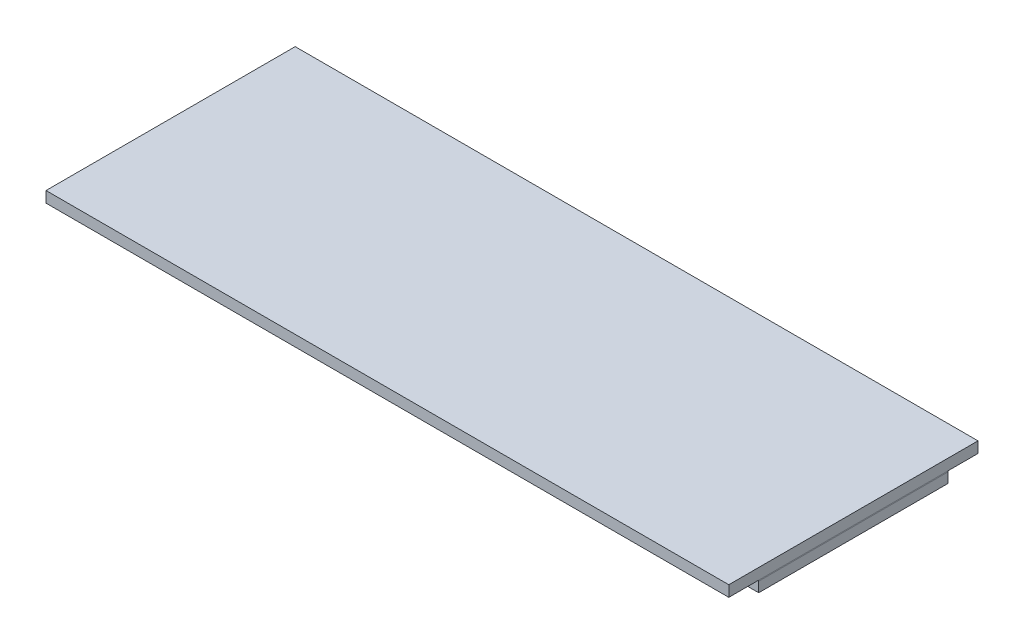
SolidWorks part; units mm, degrees
material "Glass"
ref_plane "Front Plane" through (0, 0, 0) normal (0, 0, 1) x (1, 0, 0)
ref_plane "Top Plane" through (0, 0, 0) normal (0, 1, 0) x (1, 0, 0)
ref_plane "Right Plane" through (0, 0, 0) normal (1, 0, 0) x (0, 0, -1)
sketch "Sketch1" plane through (0, 0, 0) normal (0, 1, 0) x (1, 0, 0)
  line L0 (-81.0446, 0) -> (81.0446, 0) construction
  line L1 (-34.25, 12.5) -> (34.25, 12.5)
  line L2 (-34.25, 12.5) -> (-34.25, -12.5)
  line L3 (-34.25, -12.5) -> (34.25, -12.5)
  line L4 (34.25, 12.5) -> (34.25, -12.5)
  line L5 (0, -22.2823) -> (0, 22.2823) construction
  dimension "D1" = 68.5
  dimension "D2" = 25
  dimension "D3" = 12.5
  dimension "D4" = 34.25
extrude "Boss-Extrude1" add sketch "Sketch1" along normal blind 1.1
sketch "Sketch2" plane through (0, 0, 0) normal (0, 1, 0) x (1, 0, 0)
  line L0 (-34.25, 12.5) -> (-34.25, -12.5) construction
  line L1 (-34.25, 9.5) -> (34.25, 9.5)
  line L2 (-34.25, 9.5) -> (-34.25, -9.5)
  line L3 (-34.25, -9.5) -> (34.25, -9.5)
  line L4 (34.25, 9.5) -> (34.25, -9.5)
  line L5 (34.25, -12.5) -> (34.25, 12.5) construction
  line L6 (-55, 0) -> (55, 0) construction
  dimension "D1" = 19
  dimension "D2" = 9.5
extrude "Boss-Extrude2" add sketch "Sketch2" against normal blind 0.1 separate body
sketch "Sketch3"
  dimension "D1" = 2.95
  dimension "D2" = 0.1
  dimension "D3" = 4.35
  dimension "D4" = 25.9
  dimension "D5" = 4.75
  dimension "D6" = 0.51
  dimension "D7" = 0.05
  dimension "D8" = 16
  dimension "D10" = 3.65
  dimension "D11" = 5.15
  dimension "D9" = 2
sketch "Sketch6" plane through (0, 0, 0) normal (0, 1, 0) x (1, 0, 0)
  line L1 (-27.63, -0.4) -> (-27.12, -0.4)
  line L2 (-27.63, -0.4) -> (-27.63, -0.9)
  line L3 (-27.63, -0.9) -> (-27.12, -0.9)
  line L4 (-27.12, -0.4) -> (-27.12, -0.9)
  line L5 (-27.63, -0.95) -> (-27.12, -0.95)
  line L6 (-27.63, -0.95) -> (-27.63, -1.45)
  line L7 (-27.63, -1.45) -> (-27.12, -1.45)
  line L8 (-27.12, -0.95) -> (-27.12, -1.45)
  line L9 (-27.63, -1.5) -> (-27.12, -1.5)
  line L10 (-27.63, -1.5) -> (-27.63, -2)
  line L11 (-27.63, -2) -> (-27.12, -2)
  line L12 (-27.12, -1.5) -> (-27.12, -2)
  line L13 (-27.63, -2.05) -> (-27.12, -2.05)
  line L14 (-27.63, -2.05) -> (-27.63, -2.55)
  line L15 (-27.63, -2.55) -> (-27.12, -2.55)
  line L16 (-27.12, -2.05) -> (-27.12, -2.55)
  line L17 (-27.63, -2.6) -> (-27.12, -2.6)
  line L18 (-27.63, -2.6) -> (-27.63, -3.1)
  line L19 (-27.63, -3.1) -> (-27.12, -3.1)
  line L20 (-27.12, -2.6) -> (-27.12, -3.1)
  line L21 (-27.63, -3.15) -> (-27.12, -3.15)
  line L22 (-27.63, -3.15) -> (-27.63, -3.65)
  line L23 (-27.63, -3.65) -> (-27.12, -3.65)
  line L24 (-27.12, -3.15) -> (-27.12, -3.65)
  line L25 (-27.12, -3.7) -> (-27.63, -3.7)
  line L26 (-27.12, -3.7) -> (-27.12, -4.2)
  line L27 (-27.12, -4.2) -> (-27.63, -4.2)
  line L28 (-27.63, -3.7) -> (-27.63, -4.2)
  line L29 (-28.24, -3.7) -> (-27.73, -3.7)
  line L30 (-28.24, -3.7) -> (-28.24, -4.2)
  line L31 (-28.24, -4.2) -> (-27.73, -4.2)
  line L32 (-27.73, -3.7) -> (-27.73, -4.2)
  line L33 (-27.02, -3.7) -> (-26.51, -3.7)
  line L34 (-27.02, -3.7) -> (-27.02, -4.2)
  line L35 (-27.02, -4.2) -> (-26.51, -4.2)
  line L36 (-26.51, -3.7) -> (-26.51, -4.2)
  line L37 (-28.24, -0.95) -> (-27.73, -0.95)
  line L38 (-28.24, -0.95) -> (-28.24, -1.45)
  line L39 (-28.24, -1.45) -> (-27.73, -1.45)
  line L40 (-27.73, -0.95) -> (-27.73, -1.45)
  line L41 (-22.76, -2.6) -> (-22.25, -2.6)
  line L42 (-22.76, -2.6) -> (-22.76, -3.1)
  line L43 (-22.76, -3.1) -> (-22.25, -3.1)
  line L44 (-22.25, -2.6) -> (-22.25, -3.1)
  line L45 (-22.76, -3.15) -> (-22.25, -3.15)
  line L46 (-22.76, -3.15) -> (-22.76, -3.65)
  line L47 (-22.76, -3.65) -> (-22.25, -3.65)
  line L48 (-22.25, -3.15) -> (-22.25, -3.65)
  line L49 (-23.37, -3.7) -> (-22.86, -3.7)
  line L50 (-23.37, -3.7) -> (-23.37, -4.2)
  line L51 (-23.37, -4.2) -> (-22.86, -4.2)
  line L52 (-22.86, -3.7) -> (-22.86, -4.2)
  line L53 (-23.98, -3.7) -> (-23.47, -3.7)
  line L54 (-23.98, -3.7) -> (-23.98, -4.2)
  line L55 (-23.98, -4.2) -> (-23.47, -4.2)
  line L56 (-23.47, -3.7) -> (-23.47, -4.2)
  line L57 (-24.59, -3.7) -> (-24.08, -3.7)
  line L58 (-24.59, -3.7) -> (-24.59, -4.2)
  line L59 (-24.59, -4.2) -> (-24.08, -4.2)
  line L60 (-24.08, -3.7) -> (-24.08, -4.2)
  line L61 (-25.2, -3.15) -> (-24.69, -3.15)
  line L62 (-25.2, -3.15) -> (-25.2, -3.65)
  line L63 (-25.2, -3.65) -> (-24.69, -3.65)
  line L64 (-24.69, -3.15) -> (-24.69, -3.65)
  line L65 (-25.2, -2.6) -> (-24.69, -2.6)
  line L66 (-25.2, -2.6) -> (-25.2, -3.1)
  line L67 (-25.2, -3.1) -> (-24.69, -3.1)
  line L68 (-24.69, -2.6) -> (-24.69, -3.1)
  line L69 (-25.2, -2.05) -> (-24.69, -2.05)
  line L70 (-25.2, -2.05) -> (-25.2, -2.55)
  line L71 (-25.2, -2.55) -> (-24.69, -2.55)
  line L72 (-24.69, -2.05) -> (-24.69, -2.55)
  line L73 (-23.37, -0.4) -> (-22.86, -0.4)
  line L74 (-23.37, -0.4) -> (-23.37, -0.9)
  line L75 (-23.37, -0.9) -> (-22.86, -0.9)
  line L76 (-22.86, -0.4) -> (-22.86, -0.9)
  line L77 (-23.98, -0.4) -> (-23.47, -0.4)
  line L78 (-23.98, -0.4) -> (-23.98, -0.9)
  line L79 (-23.98, -0.9) -> (-23.47, -0.9)
  line L80 (-23.47, -0.4) -> (-23.47, -0.9)
  line L81 (-24.59, -0.95) -> (-24.08, -0.95)
  line L82 (-24.59, -0.95) -> (-24.59, -1.45)
  line L83 (-24.59, -1.45) -> (-24.08, -1.45)
  line L84 (-24.08, -0.95) -> (-24.08, -1.45)
  line L85 (-25.2, -1.5) -> (-24.69, -1.5)
  line L86 (-25.2, -1.5) -> (-25.2, -2)
  line L87 (-25.2, -2) -> (-24.69, -2)
  line L88 (-24.69, -1.5) -> (-24.69, -2)
  line L89 (-24.59, -2.05) -> (-24.08, -2.05)
  line L90 (-24.59, -2.05) -> (-24.59, -2.55)
  line L91 (-24.59, -2.55) -> (-24.08, -2.55)
  line L92 (-24.08, -2.05) -> (-24.08, -2.55)
  line L93 (-23.98, -2.05) -> (-23.47, -2.05)
  line L94 (-23.98, -2.05) -> (-23.98, -2.55)
  line L95 (-23.98, -2.55) -> (-23.47, -2.55)
  line L96 (-23.47, -2.05) -> (-23.47, -2.55)
  line L97 (-23.37, -2.05) -> (-22.86, -2.05)
  line L98 (-23.37, -2.05) -> (-23.37, -2.55)
  line L99 (-23.37, -2.55) -> (-22.86, -2.55)
  line L100 (-22.86, -2.05) -> (-22.86, -2.55)
  line L101 (-21.55, -3.7) -> (-21.04, -3.7)
  line L102 (-21.55, -3.7) -> (-21.55, -4.2)
  line L103 (-21.55, -4.2) -> (-21.04, -4.2)
  line L104 (-21.04, -3.7) -> (-21.04, -4.2)
  line L105 (-20.94, -3.15) -> (-20.43, -3.15)
  line L106 (-20.94, -3.15) -> (-20.94, -3.65)
  line L107 (-20.94, -3.65) -> (-20.43, -3.65)
  line L108 (-20.43, -3.15) -> (-20.43, -3.65)
  line L109 (-20.33, -2.6) -> (-19.82, -2.6)
  line L110 (-20.33, -2.6) -> (-20.33, -3.1)
  line L111 (-20.33, -3.1) -> (-19.82, -3.1)
  line L112 (-19.82, -2.6) -> (-19.82, -3.1)
  line L113 (-19.72, -2.05) -> (-19.21, -2.05)
  line L114 (-19.72, -2.05) -> (-19.72, -2.55)
  line L115 (-19.72, -2.55) -> (-19.21, -2.55)
  line L116 (-19.21, -2.05) -> (-19.21, -2.55)
  line L117 (-19.11, -1.5) -> (-18.6, -1.5)
  line L118 (-19.11, -1.5) -> (-19.11, -2)
  line L119 (-19.11, -2) -> (-18.6, -2)
  line L120 (-18.6, -1.5) -> (-18.6, -2)
  line L121 (-20.94, -2.05) -> (-20.43, -2.05)
  line L122 (-20.94, -2.05) -> (-20.94, -2.55)
  line L123 (-20.94, -2.55) -> (-20.43, -2.55)
  line L124 (-20.43, -2.05) -> (-20.43, -2.55)
  line L125 (-21.55, -1.5) -> (-21.04, -1.5)
  line L126 (-21.55, -1.5) -> (-21.55, -2)
  line L127 (-21.55, -2) -> (-21.04, -2)
  line L128 (-21.04, -1.5) -> (-21.04, -2)
  line L129 (-19.72, -3.15) -> (-19.21, -3.15)
  line L130 (-19.72, -3.15) -> (-19.72, -3.65)
  line L131 (-19.72, -3.65) -> (-19.21, -3.65)
  line L132 (-19.21, -3.15) -> (-19.21, -3.65)
  line L133 (-19.11, -3.7) -> (-18.6, -3.7)
  line L134 (-19.11, -3.7) -> (-19.11, -4.2)
  line L135 (-19.11, -4.2) -> (-18.6, -4.2)
  line L136 (-18.6, -3.7) -> (-18.6, -4.2)
  line L137 (-17.29, -0.4) -> (-16.78, -0.4)
  line L138 (-17.29, -0.4) -> (-17.29, -0.9)
  line L139 (-17.29, -0.9) -> (-16.78, -0.9)
  line L140 (-16.78, -0.4) -> (-16.78, -0.9)
  line L141 (-16.68, -0.4) -> (-16.17, -0.4)
  line L142 (-16.68, -0.4) -> (-16.68, -0.9)
  line L143 (-16.68, -0.9) -> (-16.17, -0.9)
  line L144 (-16.17, -0.4) -> (-16.17, -0.9)
  line L145 (-16.07, -0.4) -> (-15.56, -0.4)
  line L146 (-16.07, -0.4) -> (-16.07, -0.9)
  line L147 (-16.07, -0.9) -> (-15.56, -0.9)
  line L148 (-15.56, -0.4) -> (-15.56, -0.9)
  line L149 (-15.46, -0.95) -> (-14.95, -0.95)
  line L150 (-15.46, -0.95) -> (-15.46, -1.45)
  line L151 (-15.46, -1.45) -> (-14.95, -1.45)
  line L152 (-14.95, -0.95) -> (-14.95, -1.45)
  line L153 (-15.46, -1.5) -> (-14.95, -1.5)
  line L154 (-15.46, -1.5) -> (-15.46, -2)
  line L155 (-15.46, -2) -> (-14.95, -2)
  line L156 (-14.95, -1.5) -> (-14.95, -2)
  line L157 (-16.07, -2.05) -> (-15.56, -2.05)
  line L158 (-16.07, -2.05) -> (-16.07, -2.55)
  line L159 (-16.07, -2.55) -> (-15.56, -2.55)
  line L160 (-15.56, -2.05) -> (-15.56, -2.55)
  line L161 (-16.68, -2.6) -> (-16.17, -2.6)
  line L162 (-16.68, -2.6) -> (-16.68, -3.1)
  line L163 (-16.68, -3.1) -> (-16.17, -3.1)
  line L164 (-16.17, -2.6) -> (-16.17, -3.1)
  line L165 (-17.29, -3.15) -> (-16.78, -3.15)
  line L166 (-17.29, -3.15) -> (-17.29, -3.65)
  line L167 (-17.29, -3.65) -> (-16.78, -3.65)
  line L168 (-16.78, -3.15) -> (-16.78, -3.65)
  line L169 (-17.9, -3.7) -> (-17.39, -3.7)
  line L170 (-17.9, -3.7) -> (-17.9, -4.2)
  line L171 (-17.9, -4.2) -> (-17.39, -4.2)
  line L172 (-17.39, -3.7) -> (-17.39, -4.2)
  line L173 (-17.29, -3.7) -> (-16.78, -3.7)
  line L174 (-17.29, -3.7) -> (-17.29, -4.2)
  line L175 (-17.29, -4.2) -> (-16.78, -4.2)
  line L176 (-16.78, -3.7) -> (-16.78, -4.2)
  line L177 (-16.68, -3.7) -> (-16.17, -3.7)
  line L178 (-16.68, -3.7) -> (-16.68, -4.2)
  line L179 (-16.68, -4.2) -> (-16.17, -4.2)
  line L180 (-16.17, -3.7) -> (-16.17, -4.2)
  line L181 (-16.07, -4.2) -> (-15.56, -4.2)
  line L182 (-16.07, -4.2) -> (-16.07, -3.7)
  line L183 (-16.07, -3.7) -> (-15.56, -3.7)
  line L184 (-15.56, -4.2) -> (-15.56, -3.7)
  line L185 (-15.46, -4.2) -> (-14.95, -4.2)
  line L186 (-15.46, -4.2) -> (-15.46, -3.7)
  line L187 (-15.46, -3.7) -> (-14.95, -3.7)
  line L188 (-14.95, -4.2) -> (-14.95, -3.7)
  line L189 (-17.9, -0.95) -> (-17.39, -0.95)
  line L190 (-17.9, -0.95) -> (-17.9, -1.45)
  line L191 (-17.9, -1.45) -> (-17.39, -1.45)
  line L192 (-17.39, -0.95) -> (-17.39, -1.45)
  line L193 (-10.6, -0.4) -> (-10.09, -0.4)
  line L194 (-10.6, -0.4) -> (-10.6, -0.9)
  line L195 (-10.6, -0.9) -> (-10.09, -0.9)
  line L196 (-10.09, -0.4) -> (-10.09, -0.9)
  line L197 (-10.6, -0.95) -> (-10.09, -0.95)
  line L198 (-10.6, -0.95) -> (-10.6, -1.45)
  line L199 (-10.6, -1.45) -> (-10.09, -1.45)
  line L200 (-10.09, -0.95) -> (-10.09, -1.45)
  line L201 (-10.6, -1.5) -> (-10.09, -1.5)
  line L202 (-10.6, -1.5) -> (-10.6, -2)
  line L203 (-10.6, -2) -> (-10.09, -2)
  line L204 (-10.09, -1.5) -> (-10.09, -2)
  line L205 (-10.6, -2.05) -> (-10.09, -2.05)
  line L206 (-10.6, -2.05) -> (-10.6, -2.55)
  line L207 (-10.6, -2.55) -> (-10.09, -2.55)
  line L208 (-10.09, -2.05) -> (-10.09, -2.55)
  line L209 (-10.6, -2.6) -> (-10.09, -2.6)
  line L210 (-10.6, -2.6) -> (-10.6, -3.1)
  line L211 (-10.6, -3.1) -> (-10.09, -3.1)
  line L212 (-10.09, -2.6) -> (-10.09, -3.1)
  line L213 (-10.6, -3.15) -> (-10.09, -3.15)
  line L214 (-10.6, -3.15) -> (-10.6, -3.65)
  line L215 (-10.6, -3.65) -> (-10.09, -3.65)
  line L216 (-10.09, -3.15) -> (-10.09, -3.65)
  line L217 (-10.6, -3.7) -> (-10.09, -3.7)
  line L218 (-10.6, -3.7) -> (-10.6, -4.2)
  line L219 (-10.6, -4.2) -> (-10.09, -4.2)
  line L220 (-10.09, -3.7) -> (-10.09, -4.2)
  line L221 (-9.99, -3.7) -> (-9.48, -3.7)
  line L222 (-9.99, -3.7) -> (-9.99, -4.2)
  line L223 (-9.99, -4.2) -> (-9.48, -4.2)
  line L224 (-9.48, -3.7) -> (-9.48, -4.2)
  line L225 (-9.38, -3.7) -> (-8.87, -3.7)
  line L226 (-9.38, -3.7) -> (-9.38, -4.2)
  line L227 (-9.38, -4.2) -> (-8.87, -4.2)
  line L228 (-8.87, -3.7) -> (-8.87, -4.2)
  line L229 (-8.77, -3.7) -> (-8.26, -3.7)
  line L230 (-8.77, -3.7) -> (-8.77, -4.2)
  line L231 (-8.77, -4.2) -> (-8.26, -4.2)
  line L232 (-8.26, -3.7) -> (-8.26, -4.2)
  line L233 (-8.16, -3.7) -> (-7.65, -3.7)
  line L234 (-8.16, -3.7) -> (-8.16, -4.2)
  line L235 (-8.16, -4.2) -> (-7.65, -4.2)
  line L236 (-7.65, -3.7) -> (-7.65, -4.2)
  line L237 (-6.34, -0.4) -> (-5.83, -0.4)
  line L238 (-6.34, -0.4) -> (-6.34, -0.9)
  line L239 (-6.34, -0.9) -> (-5.83, -0.9)
  line L240 (-5.83, -0.4) -> (-5.83, -0.9)
  line L241 (-5.73, -0.4) -> (-5.22, -0.4)
  line L242 (-5.73, -0.4) -> (-5.73, -0.9)
  line L243 (-5.73, -0.9) -> (-5.22, -0.9)
  line L244 (-5.22, -0.4) -> (-5.22, -0.9)
  line L245 (-5.12, -0.4) -> (-4.61, -0.4)
  line L246 (-5.12, -0.4) -> (-5.12, -0.9)
  line L247 (-5.12, -0.9) -> (-4.61, -0.9)
  line L248 (-4.61, -0.4) -> (-4.61, -0.9)
  line L249 (-4.51, -0.95) -> (-4, -0.95)
  line L250 (-4.51, -0.95) -> (-4.51, -1.45)
  line L251 (-4.51, -1.45) -> (-4, -1.45)
  line L252 (-4, -0.95) -> (-4, -1.45)
  line L253 (-6.95, -0.95) -> (-6.44, -0.95)
  line L254 (-6.95, -0.95) -> (-6.95, -1.45)
  line L255 (-6.95, -1.45) -> (-6.44, -1.45)
  line L256 (-6.44, -0.95) -> (-6.44, -1.45)
  line L257 (-6.95, -1.5) -> (-6.44, -1.5)
  line L258 (-6.95, -1.5) -> (-6.95, -2)
  line L259 (-6.95, -2) -> (-6.44, -2)
  line L260 (-6.44, -1.5) -> (-6.44, -2)
  line L261 (-6.95, -2.05) -> (-6.44, -2.05)
  line L262 (-6.95, -2.05) -> (-6.95, -2.55)
  line L263 (-6.95, -2.55) -> (-6.44, -2.55)
  line L264 (-6.44, -2.05) -> (-6.44, -2.55)
  line L265 (-6.95, -2.6) -> (-6.44, -2.6)
  line L266 (-6.95, -2.6) -> (-6.95, -3.1)
  line L267 (-6.95, -3.1) -> (-6.44, -3.1)
  line L268 (-6.44, -2.6) -> (-6.44, -3.1)
  line L269 (-6.95, -3.15) -> (-6.44, -3.15)
  line L270 (-6.95, -3.15) -> (-6.95, -3.65)
  line L271 (-6.95, -3.65) -> (-6.44, -3.65)
  line L272 (-6.44, -3.15) -> (-6.44, -3.65)
  line L273 (-6.34, -3.7) -> (-5.83, -3.7)
  line L274 (-6.34, -3.7) -> (-6.34, -4.2)
  line L275 (-6.34, -4.2) -> (-5.83, -4.2)
  line L276 (-5.83, -3.7) -> (-5.83, -4.2)
  line L277 (-5.73, -4.2) -> (-5.22, -4.2)
  line L278 (-5.73, -4.2) -> (-5.73, -3.7)
  line L279 (-5.73, -3.7) -> (-5.22, -3.7)
  line L280 (-5.22, -4.2) -> (-5.22, -3.7)
  line L281 (-5.12, -3.7) -> (-4.61, -3.7)
  line L282 (-5.12, -3.7) -> (-5.12, -4.2)
  line L283 (-5.12, -4.2) -> (-4.61, -4.2)
  line L284 (-4.61, -3.7) -> (-4.61, -4.2)
  line L285 (-4.51, -3.15) -> (-4, -3.15)
  line L286 (-4.51, -3.15) -> (-4.51, -3.65)
  line L287 (-4.51, -3.65) -> (-4, -3.65)
  line L288 (-4, -3.15) -> (-4, -3.65)
  line L289 (-3.3, -0.4) -> (-2.79, -0.4)
  line L290 (-3.3, -0.4) -> (-3.3, -0.9)
  line L291 (-3.3, -0.9) -> (-2.79, -0.9)
  line L292 (-2.79, -0.4) -> (-2.79, -0.9)
  line L293 (-2.69, -0.4) -> (-2.18, -0.4)
  line L294 (-2.69, -0.4) -> (-2.69, -0.9)
  line L295 (-2.69, -0.9) -> (-2.18, -0.9)
  line L296 (-2.18, -0.4) -> (-2.18, -0.9)
  line L297 (-2.08, -0.4) -> (-1.57, -0.4)
  line L298 (-2.08, -0.4) -> (-2.08, -0.9)
  line L299 (-2.08, -0.9) -> (-1.57, -0.9)
  line L300 (-1.57, -0.4) -> (-1.57, -0.9)
  line L301 (-1.47, -0.95) -> (-0.96, -0.95)
  line L302 (-1.47, -0.95) -> (-1.47, -1.45)
  line L303 (-1.47, -1.45) -> (-0.96, -1.45)
  line L304 (-0.96, -0.95) -> (-0.96, -1.45)
  line L305 (-0.86, -1.5) -> (-0.35, -1.5)
  line L306 (-0.86, -1.5) -> (-0.86, -2)
  line L307 (-0.86, -2) -> (-0.35, -2)
  line L308 (-0.35, -1.5) -> (-0.35, -2)
  line L309 (-3.3, -0.95) -> (-2.79, -0.95)
  line L310 (-3.3, -0.95) -> (-3.3, -1.45)
  line L311 (-3.3, -1.45) -> (-2.79, -1.45)
  line L312 (-2.79, -0.95) -> (-2.79, -1.45)
  line L313 (-3.3, -1.5) -> (-2.79, -1.5)
  line L314 (-3.3, -1.5) -> (-3.3, -2)
  line L315 (-3.3, -2) -> (-2.79, -2)
  line L316 (-2.79, -1.5) -> (-2.79, -2)
  line L317 (-3.3, -2.05) -> (-2.79, -2.05)
  line L318 (-3.3, -2.05) -> (-3.3, -2.55)
  line L319 (-3.3, -2.55) -> (-2.79, -2.55)
  line L320 (-2.79, -2.05) -> (-2.79, -2.55)
  line L321 (-3.3, -2.6) -> (-2.79, -2.6)
  line L322 (-3.3, -2.6) -> (-3.3, -3.1)
  line L323 (-3.3, -3.1) -> (-2.79, -3.1)
  line L324 (-2.79, -2.6) -> (-2.79, -3.1)
  line L325 (-3.3, -3.15) -> (-2.79, -3.15)
  line L326 (-3.3, -3.15) -> (-3.3, -3.65)
  line L327 (-3.3, -3.65) -> (-2.79, -3.65)
  line L328 (-2.79, -3.15) -> (-2.79, -3.65)
  line L329 (-3.3, -3.7) -> (-2.79, -3.7)
  line L330 (-3.3, -3.7) -> (-3.3, -4.2)
  line L331 (-3.3, -4.2) -> (-2.79, -4.2)
  line L332 (-2.79, -3.7) -> (-2.79, -4.2)
  line L333 (-2.69, -4.2) -> (-2.18, -4.2)
  line L334 (-2.69, -4.2) -> (-2.69, -3.7)
  line L335 (-2.69, -3.7) -> (-2.18, -3.7)
  line L336 (-2.18, -4.2) -> (-2.18, -3.7)
  line L337 (-2.08, -4.2) -> (-1.57, -4.2)
  line L338 (-2.08, -4.2) -> (-2.08, -3.7)
  line L339 (-2.08, -3.7) -> (-1.57, -3.7)
  line L340 (-1.57, -4.2) -> (-1.57, -3.7)
  line L349 (-1.47, -3.15) -> (-0.96, -3.15)
  line L350 (-1.47, -3.15) -> (-1.47, -3.65)
  line L351 (-1.47, -3.65) -> (-0.96, -3.65)
  line L352 (-0.96, -3.15) -> (-0.96, -3.65)
  line L353 (-0.86, -2.6) -> (-0.35, -2.6)
  line L354 (-0.86, -2.6) -> (-0.86, -3.1)
  line L355 (-0.86, -3.1) -> (-0.35, -3.1)
  line L356 (-0.35, -2.6) -> (-0.35, -3.1)
  line L357 (-0.86, -2.05) -> (-0.35, -2.05)
  line L358 (-0.86, -2.05) -> (-0.86, -2.55)
  line L359 (-0.86, -2.55) -> (-0.35, -2.55)
  line L360 (-0.35, -2.05) -> (-0.35, -2.55)
  point P458 (0, 0)
  point P459 (0, 0)
extrude "16x2 LCD" cut sketch "Sketch6" against normal blind 1
sketch "Sketch7" plane through (0, 0, 0) normal (0, 1, 0) x (1, 0, 0)
  line L0 (12.52, -2) -> (13.03, -2) construction
  line L1 (4, -0.4) -> (4.51, -0.4)
  line L2 (4, -0.4) -> (4, -0.9)
  line L3 (4, -0.9) -> (4.51, -0.9)
  line L4 (4.51, -0.4) -> (4.51, -0.9)
  line L5 (4.61, -0.4) -> (5.12, -0.4)
  line L6 (4.61, -0.4) -> (4.61, -0.9)
  line L7 (4.61, -0.9) -> (5.12, -0.9)
  line L8 (5.12, -0.4) -> (5.12, -0.9)
  line L9 (5.22, -0.4) -> (5.73, -0.4)
  line L10 (5.22, -0.4) -> (5.22, -0.9)
  line L11 (5.22, -0.9) -> (5.73, -0.9)
  line L12 (5.73, -0.4) -> (5.73, -0.9)
  line L13 (5.83, -0.95) -> (6.34, -0.95)
  line L14 (5.83, -0.95) -> (5.83, -1.45)
  line L15 (5.83, -1.45) -> (6.34, -1.45)
  line L16 (6.34, -0.95) -> (6.34, -1.45)
  line L17 (6.44, -1.5) -> (6.95, -1.5)
  line L18 (6.44, -1.5) -> (6.44, -2)
  line L19 (6.44, -2) -> (6.95, -2)
  line L20 (6.95, -1.5) -> (6.95, -2)
  line L21 (6.44, -2.05) -> (6.95, -2.05)
  line L22 (6.44, -2.05) -> (6.44, -2.55)
  line L23 (6.44, -2.55) -> (6.95, -2.55)
  line L24 (6.95, -2.05) -> (6.95, -2.55)
  line L25 (6.44, -2.6) -> (6.95, -2.6)
  line L26 (6.44, -2.6) -> (6.44, -3.1)
  line L27 (6.44, -3.1) -> (6.95, -3.1)
  line L28 (6.95, -2.6) -> (6.95, -3.1)
  line L29 (5.83, -3.15) -> (6.34, -3.15)
  line L30 (5.83, -3.15) -> (5.83, -3.65)
  line L31 (5.83, -3.65) -> (6.34, -3.65)
  line L32 (6.34, -3.15) -> (6.34, -3.65)
  line L33 (5.22, -3.7) -> (5.73, -3.7)
  line L34 (5.22, -3.7) -> (5.22, -4.2)
  line L35 (5.22, -4.2) -> (5.73, -4.2)
  line L36 (5.73, -3.7) -> (5.73, -4.2)
  line L37 (4.61, -3.7) -> (5.12, -3.7)
  line L38 (4.61, -3.7) -> (4.61, -4.2)
  line L39 (4.61, -4.2) -> (5.12, -4.2)
  line L40 (5.12, -3.7) -> (5.12, -4.2)
  line L41 (4, -3.7) -> (4.51, -3.7)
  line L42 (4, -3.7) -> (4, -4.2)
  line L43 (4, -4.2) -> (4.51, -4.2)
  line L44 (4.51, -3.7) -> (4.51, -4.2)
  line L45 (4, -3.15) -> (4.51, -3.15)
  line L46 (4, -3.15) -> (4, -3.65)
  line L47 (4, -3.65) -> (4.51, -3.65)
  line L48 (4.51, -3.15) -> (4.51, -3.65)
  line L49 (4, -2.6) -> (4.51, -2.6)
  line L50 (4, -2.6) -> (4, -3.1)
  line L51 (4, -3.1) -> (4.51, -3.1)
  line L52 (4.51, -2.6) -> (4.51, -3.1)
  line L53 (4, -2.05) -> (4.51, -2.05)
  line L54 (4, -2.05) -> (4, -2.55)
  line L55 (4, -2.55) -> (4.51, -2.55)
  line L56 (4.51, -2.05) -> (4.51, -2.55)
  line L57 (4, -1.5) -> (4.51, -1.5)
  line L58 (4, -1.5) -> (4, -2)
  line L59 (4, -2) -> (4.51, -2)
  line L60 (4.51, -1.5) -> (4.51, -2)
  line L61 (4, -0.95) -> (4.51, -0.95)
  line L62 (4, -0.95) -> (4, -1.45)
  line L63 (4, -1.45) -> (4.51, -1.45)
  line L64 (4.51, -0.95) -> (4.51, -1.45)
  line L65 (8.87, -0.4) -> (9.38, -0.4)
  line L66 (8.87, -0.4) -> (8.87, -0.9)
  line L67 (8.87, -0.9) -> (9.38, -0.9)
  line L68 (9.38, -0.4) -> (9.38, -0.9)
  line L69 (8.87, -1.5) -> (9.38, -1.5)
  line L70 (8.87, -1.5) -> (8.87, -2)
  line L71 (8.87, -2) -> (9.38, -2)
  line L72 (9.38, -1.5) -> (9.38, -2)
  line L73 (8.26, -1.5) -> (8.77, -1.5)
  line L74 (8.26, -1.5) -> (8.26, -2)
  line L75 (8.26, -2) -> (8.77, -2)
  line L76 (8.77, -1.5) -> (8.77, -2)
  line L77 (8.87, -2.05) -> (9.38, -2.05)
  line L78 (8.87, -2.05) -> (8.87, -2.55)
  line L79 (8.87, -2.55) -> (9.38, -2.55)
  line L80 (9.38, -2.05) -> (9.38, -2.55)
  line L81 (8.87, -2.6) -> (9.38, -2.6)
  line L82 (8.87, -2.6) -> (8.87, -3.1)
  line L83 (8.87, -3.1) -> (9.38, -3.1)
  line L84 (9.38, -2.6) -> (9.38, -3.1)
  line L85 (8.87, -3.15) -> (9.38, -3.15)
  line L86 (8.87, -3.15) -> (8.87, -3.65)
  line L87 (8.87, -3.65) -> (9.38, -3.65)
  line L88 (9.38, -3.15) -> (9.38, -3.65)
  line L89 (8.26, -3.7) -> (8.77, -3.7)
  line L90 (8.26, -3.7) -> (8.26, -4.2)
  line L91 (8.26, -4.2) -> (8.77, -4.2)
  line L92 (8.77, -3.7) -> (8.77, -4.2)
  line L93 (8.87, -3.7) -> (9.38, -3.7)
  line L94 (8.87, -3.7) -> (8.87, -4.2)
  line L95 (8.87, -4.2) -> (9.38, -4.2)
  line L96 (9.38, -3.7) -> (9.38, -4.2)
  line L97 (9.48, -3.7) -> (9.99, -3.7)
  line L98 (9.48, -3.7) -> (9.48, -4.2)
  line L99 (9.48, -4.2) -> (9.99, -4.2)
  line L100 (9.99, -3.7) -> (9.99, -4.2)
  line L101 (11.91, -1.5) -> (12.42, -1.5)
  line L102 (11.91, -1.5) -> (11.91, -2)
  line L103 (11.91, -2) -> (12.42, -2)
  line L104 (12.42, -1.5) -> (12.42, -2)
  line L105 (12.52, -1.5) -> (13.03, -1.5)
  line L106 (12.52, -1.5) -> (12.52, -2)
  line L107 (12.52, -2) -> (13.03, -2)
  line L108 (13.03, -1.5) -> (13.03, -2)
  line L110 (13.13, -1.5) -> (13.64, -1.5)
  line L111 (13.13, -1.5) -> (13.13, -2)
  line L112 (13.13, -2) -> (13.64, -2)
  line L113 (13.64, -1.5) -> (13.64, -2)
  line L114 (11.91, -2.6) -> (12.42, -2.6)
  line L115 (11.91, -2.6) -> (11.91, -3.1)
  line L116 (11.91, -3.1) -> (12.42, -3.1)
  line L117 (12.42, -2.6) -> (12.42, -3.1)
  line L118 (12.52, -2.6) -> (13.03, -2.6)
  line L119 (12.52, -2.6) -> (12.52, -3.1)
  line L120 (12.52, -3.1) -> (13.03, -3.1)
  line L121 (13.03, -2.6) -> (13.03, -3.1)
  line L122 (13.13, -2.6) -> (13.64, -2.6)
  line L123 (13.13, -2.6) -> (13.13, -3.1)
  line L124 (13.13, -3.1) -> (13.64, -3.1)
  line L125 (13.64, -2.6) -> (13.64, -3.1)
  line L126 (13.64, -3.7) -> (13.13, -3.7)
  line L127 (13.64, -3.7) -> (13.64, -4.2)
  line L128 (13.64, -4.2) -> (13.13, -4.2)
  line L129 (13.13, -3.7) -> (13.13, -4.2)
  line L130 (13.03, -3.7) -> (12.52, -3.7)
  line L131 (13.03, -3.7) -> (13.03, -4.2)
  line L132 (13.03, -4.2) -> (12.52, -4.2)
  line L133 (12.52, -3.7) -> (12.52, -4.2)
  line L134 (11.91, -3.7) -> (12.42, -3.7)
  line L135 (11.91, -3.7) -> (11.91, -4.2)
  line L136 (11.91, -4.2) -> (12.42, -4.2)
  line L137 (12.42, -3.7) -> (12.42, -4.2)
  line L138 (11.3, -2.05) -> (11.81, -2.05)
  line L139 (11.3, -2.05) -> (11.3, -2.55)
  line L140 (11.3, -2.55) -> (11.81, -2.55)
  line L141 (11.81, -2.05) -> (11.81, -2.55)
  line L142 (13.74, -3.15) -> (14.25, -3.15)
  line L143 (13.74, -3.15) -> (13.74, -3.65)
  line L144 (13.74, -3.65) -> (14.25, -3.65)
  line L145 (14.25, -3.15) -> (14.25, -3.65)
  line L146 (11.3, -3.7) -> (11.81, -3.7)
  line L147 (11.3, -3.7) -> (11.3, -4.2)
  line L148 (11.3, -4.2) -> (11.81, -4.2)
  line L149 (11.81, -3.7) -> (11.81, -4.2)
  line L150 (14.95, -4.25) -> (15.46, -4.25)
  line L151 (14.95, -4.25) -> (14.95, -4.75)
  line L152 (14.95, -4.75) -> (15.46, -4.75)
  line L153 (15.46, -4.25) -> (15.46, -4.75)
  line L154 (14.95, -3.7) -> (15.46, -3.7)
  line L155 (14.95, -3.7) -> (14.95, -4.2)
  line L156 (14.95, -4.2) -> (15.46, -4.2)
  line L157 (15.46, -3.7) -> (15.46, -4.2)
  line L158 (14.95, -3.15) -> (15.46, -3.15)
  line L159 (14.95, -3.15) -> (14.95, -3.65)
  line L160 (14.95, -3.65) -> (15.46, -3.65)
  line L161 (15.46, -3.15) -> (15.46, -3.65)
  line L162 (14.95, -2.6) -> (15.46, -2.6)
  line L163 (14.95, -2.6) -> (14.95, -3.1)
  line L164 (14.95, -3.1) -> (15.46, -3.1)
  line L165 (15.46, -2.6) -> (15.46, -3.1)
  line L166 (14.95, -2.05) -> (15.46, -2.05)
  line L167 (14.95, -2.05) -> (14.95, -2.55)
  line L168 (14.95, -2.55) -> (15.46, -2.55)
  line L169 (15.46, -2.05) -> (15.46, -2.55)
  line L170 (14.95, -1.5) -> (15.46, -1.5)
  line L171 (14.95, -1.5) -> (14.95, -2)
  line L172 (14.95, -2) -> (15.46, -2)
  line L173 (15.46, -1.5) -> (15.46, -2)
  line L174 (15.56, -2.05) -> (16.07, -2.05)
  line L175 (15.56, -2.05) -> (15.56, -2.55)
  line L176 (15.56, -2.55) -> (16.07, -2.55)
  line L177 (16.07, -2.05) -> (16.07, -2.55)
  line L178 (16.17, -1.5) -> (16.68, -1.5)
  line L179 (16.17, -1.5) -> (16.17, -2)
  line L180 (16.17, -2) -> (16.68, -2)
  line L181 (16.68, -1.5) -> (16.68, -2)
  line L182 (16.78, -1.5) -> (17.29, -1.5)
  line L183 (16.78, -1.5) -> (16.78, -2)
  line L184 (16.78, -2) -> (17.29, -2)
  line L185 (17.29, -1.5) -> (17.29, -2)
  line L186 (17.39, -2.05) -> (17.9, -2.05)
  line L187 (17.39, -2.05) -> (17.39, -2.55)
  line L188 (17.39, -2.55) -> (17.9, -2.55)
  line L189 (17.9, -2.05) -> (17.9, -2.55)
  line L190 (17.39, -2.6) -> (17.9, -2.6)
  line L191 (17.39, -2.6) -> (17.39, -3.1)
  line L192 (17.39, -3.1) -> (17.9, -3.1)
  line L193 (17.9, -2.6) -> (17.9, -3.1)
  line L194 (15.56, -3.15) -> (16.07, -3.15)
  line L195 (15.56, -3.15) -> (15.56, -3.65)
  line L196 (15.56, -3.65) -> (16.07, -3.65)
  line L197 (16.07, -3.15) -> (16.07, -3.65)
  line L198 (16.17, -3.15) -> (16.68, -3.15)
  line L199 (16.17, -3.15) -> (16.17, -3.65)
  line L200 (16.17, -3.65) -> (16.68, -3.65)
  line L201 (16.68, -3.15) -> (16.68, -3.65)
  line L202 (16.78, -3.15) -> (17.29, -3.15)
  line L203 (16.78, -3.15) -> (16.78, -3.65)
  line L204 (16.78, -3.65) -> (17.29, -3.65)
  line L205 (17.29, -3.15) -> (17.29, -3.65)
  line L206 (19.21, -0.4) -> (19.72, -0.4)
  line L207 (19.21, -0.4) -> (19.21, -0.9)
  line L208 (19.21, -0.9) -> (19.72, -0.9)
  line L209 (19.72, -0.4) -> (19.72, -0.9)
  line L210 (19.82, -0.4) -> (20.33, -0.4)
  line L211 (19.82, -0.4) -> (19.82, -0.9)
  line L212 (19.82, -0.9) -> (20.33, -0.9)
  line L213 (20.33, -0.4) -> (20.33, -0.9)
  line L214 (19.82, -0.95) -> (20.33, -0.95)
  line L215 (19.82, -0.95) -> (19.82, -1.45)
  line L216 (19.82, -1.45) -> (20.33, -1.45)
  line L217 (20.33, -0.95) -> (20.33, -1.45)
  line L218 (19.82, -1.5) -> (20.33, -1.5)
  line L219 (19.82, -1.5) -> (19.82, -2)
  line L220 (19.82, -2) -> (20.33, -2)
  line L221 (20.33, -1.5) -> (20.33, -2)
  line L222 (19.82, -2.55) -> (20.33, -2.55)
  line L223 (19.82, -2.55) -> (19.82, -2.05)
  line L224 (19.82, -2.05) -> (20.33, -2.05)
  line L225 (20.33, -2.55) -> (20.33, -2.05)
  line L226 (19.82, -3.1) -> (20.33, -3.1)
  line L227 (19.82, -3.1) -> (19.82, -2.6)
  line L228 (19.82, -2.6) -> (20.33, -2.6)
  line L229 (20.33, -3.1) -> (20.33, -2.6)
  line L230 (19.82, -3.65) -> (20.33, -3.65)
  line L231 (19.82, -3.65) -> (19.82, -3.15)
  line L232 (19.82, -3.15) -> (20.33, -3.15)
  line L233 (20.33, -3.65) -> (20.33, -3.15)
  line L234 (19.21, -3.7) -> (19.72, -3.7)
  line L235 (19.21, -3.7) -> (19.21, -4.2)
  line L236 (19.21, -4.2) -> (19.72, -4.2)
  line L237 (19.72, -3.7) -> (19.72, -4.2)
  line L238 (19.82, -3.7) -> (20.33, -3.7)
  line L239 (19.82, -3.7) -> (19.82, -4.2)
  line L240 (19.82, -4.2) -> (20.33, -4.2)
  line L241 (20.33, -3.7) -> (20.33, -4.2)
  line L242 (20.43, -3.7) -> (20.94, -3.7)
  line L243 (20.43, -3.7) -> (20.43, -4.2)
  line L244 (20.43, -4.2) -> (20.94, -4.2)
  line L245 (20.94, -3.7) -> (20.94, -4.2)
  line L246 (22.86, -1.5) -> (23.37, -1.5)
  line L247 (22.86, -1.5) -> (22.86, -2)
  line L248 (22.86, -2) -> (23.37, -2)
  line L249 (23.37, -1.5) -> (23.37, -2)
  line L250 (23.47, -1.5) -> (23.98, -1.5)
  line L251 (23.47, -1.5) -> (23.47, -2)
  line L252 (23.47, -2) -> (23.98, -2)
  line L253 (23.98, -1.5) -> (23.98, -2)
  line L254 (24.08, -1.5) -> (24.59, -1.5)
  line L255 (24.08, -1.5) -> (24.08, -2)
  line L256 (24.08, -2) -> (24.59, -2)
  line L257 (24.59, -1.5) -> (24.59, -2)
  line L258 (24.69, -2.05) -> (25.2, -2.05)
  line L259 (24.69, -2.05) -> (24.69, -2.55)
  line L260 (24.69, -2.55) -> (25.2, -2.55)
  line L261 (25.2, -2.05) -> (25.2, -2.55)
  line L262 (24.69, -2.6) -> (25.2, -2.6)
  line L263 (24.69, -2.6) -> (24.69, -3.1)
  line L264 (24.69, -3.1) -> (25.2, -3.1)
  line L265 (25.2, -2.6) -> (25.2, -3.1)
  line L266 (24.69, -3.15) -> (25.2, -3.15)
  line L267 (24.69, -3.15) -> (24.69, -3.65)
  line L268 (24.69, -3.65) -> (25.2, -3.65)
  line L269 (25.2, -3.15) -> (25.2, -3.65)
  line L270 (24.69, -3.7) -> (25.2, -3.7)
  line L271 (24.69, -3.7) -> (24.69, -4.2)
  line L272 (24.69, -4.2) -> (25.2, -4.2)
  line L273 (25.2, -3.7) -> (25.2, -4.2)
  line L274 (24.08, -3.7) -> (24.59, -3.7)
  line L275 (24.08, -3.7) -> (24.08, -4.2)
  line L276 (24.08, -4.2) -> (24.59, -4.2)
  line L277 (24.59, -3.7) -> (24.59, -4.2)
  line L278 (23.47, -3.7) -> (23.98, -3.7)
  line L279 (23.47, -3.7) -> (23.47, -4.2)
  line L280 (23.47, -4.2) -> (23.98, -4.2)
  line L281 (23.98, -3.7) -> (23.98, -4.2)
  line L282 (22.86, -3.7) -> (23.37, -3.7)
  line L283 (22.86, -3.7) -> (22.86, -4.2)
  line L284 (22.86, -4.2) -> (23.37, -4.2)
  line L285 (23.37, -3.7) -> (23.37, -4.2)
  line L286 (22.25, -3.15) -> (22.76, -3.15)
  line L287 (22.25, -3.15) -> (22.25, -3.65)
  line L288 (22.25, -3.65) -> (22.76, -3.65)
  line L289 (22.76, -3.15) -> (22.76, -3.65)
  line L290 (22.86, -2.6) -> (23.37, -2.6)
  line L291 (22.86, -2.6) -> (22.86, -3.1)
  line L292 (22.86, -3.1) -> (23.37, -3.1)
  line L293 (23.37, -2.6) -> (23.37, -3.1)
  line L294 (23.47, -2.6) -> (23.98, -2.6)
  line L295 (23.47, -2.6) -> (23.47, -3.1)
  line L296 (23.47, -3.1) -> (23.98, -3.1)
  line L297 (23.98, -2.6) -> (23.98, -3.1)
  line L298 (24.08, -2.6) -> (24.59, -2.6)
  line L299 (24.08, -2.6) -> (24.08, -3.1)
  line L300 (24.08, -3.1) -> (24.59, -3.1)
  line L301 (24.59, -2.6) -> (24.59, -3.1)
  line L302 (25.9, -1.5) -> (26.41, -1.5)
  line L303 (25.9, -1.5) -> (25.9, -2)
  line L304 (25.9, -2) -> (26.41, -2)
  line L305 (26.41, -1.5) -> (26.41, -2)
  line L306 (26.51, -4.25) -> (27.02, -4.25)
  line L307 (26.51, -4.25) -> (26.51, -4.75)
  line L308 (26.51, -4.75) -> (27.02, -4.75)
  line L309 (27.02, -4.25) -> (27.02, -4.75)
  line L310 (27.12, -4.25) -> (27.63, -4.25)
  line L311 (27.12, -4.25) -> (27.12, -4.75)
  line L312 (27.12, -4.75) -> (27.63, -4.75)
  line L313 (27.63, -4.25) -> (27.63, -4.75)
  line L314 (27.73, -4.25) -> (28.24, -4.25)
  line L315 (27.73, -4.25) -> (27.73, -4.75)
  line L316 (27.73, -4.75) -> (28.24, -4.75)
  line L317 (28.24, -4.25) -> (28.24, -4.75)
  line L318 (28.34, -3.7) -> (28.85, -3.7)
  line L319 (28.34, -3.7) -> (28.34, -4.2)
  line L320 (28.34, -4.2) -> (28.85, -4.2)
  line L321 (28.85, -3.7) -> (28.85, -4.2)
  line L322 (28.34, -3.15) -> (28.85, -3.15)
  line L323 (28.34, -3.15) -> (28.34, -3.65)
  line L324 (28.34, -3.65) -> (28.85, -3.65)
  line L325 (28.85, -3.15) -> (28.85, -3.65)
  line L326 (28.34, -2.6) -> (28.85, -2.6)
  line L327 (28.34, -2.6) -> (28.34, -3.1)
  line L328 (28.34, -3.1) -> (28.85, -3.1)
  line L329 (28.85, -2.6) -> (28.85, -3.1)
  line L330 (28.34, -2.05) -> (28.85, -2.05)
  line L331 (28.34, -2.05) -> (28.34, -2.55)
  line L332 (28.34, -2.55) -> (28.85, -2.55)
  line L333 (28.85, -2.05) -> (28.85, -2.55)
  line L334 (28.34, -1.5) -> (28.85, -1.5)
  line L335 (28.34, -1.5) -> (28.34, -2)
  line L336 (28.34, -2) -> (28.85, -2)
  line L337 (28.85, -1.5) -> (28.85, -2)
  line L338 (27.73, -3.15) -> (28.24, -3.15)
  line L339 (27.73, -3.15) -> (27.73, -3.65)
  line L340 (27.73, -3.65) -> (28.24, -3.65)
  line L341 (28.24, -3.15) -> (28.24, -3.65)
  line L342 (27.12, -3.15) -> (27.63, -3.15)
  line L343 (27.12, -3.15) -> (27.12, -3.65)
  line L344 (27.12, -3.65) -> (27.63, -3.65)
  line L345 (27.63, -3.15) -> (27.63, -3.65)
  line L346 (26.51, -3.15) -> (27.02, -3.15)
  line L347 (26.51, -3.15) -> (26.51, -3.65)
  line L348 (26.51, -3.65) -> (27.02, -3.65)
  line L349 (27.02, -3.15) -> (27.02, -3.65)
  line L350 (25.9, -2.6) -> (26.41, -2.6)
  line L351 (25.9, -2.6) -> (25.9, -3.1)
  line L352 (25.9, -3.1) -> (26.41, -3.1)
  line L353 (26.41, -2.6) -> (26.41, -3.1)
  line L354 (25.9, -2.05) -> (26.41, -2.05)
  line L355 (25.9, -2.05) -> (25.9, -2.55)
  line L356 (25.9, -2.55) -> (26.41, -2.55)
  line L357 (26.41, -2.05) -> (26.41, -2.55)
extrude "Display" cut sketch "Sketch7" against normal blind 1
sketch "Sketch4" plane through (0, -0.1, 0) normal (0, -1, 0) x (1, 0, 0)
  line L0 (34.25, 12.5) -> (34.25, -12.5) construction
  line L1 (-34.25, 9.5) -> (34.25, 9.5)
  line L2 (-34.25, 9.5) -> (-34.25, -9.5)
  line L3 (-34.25, -9.5) -> (34.25, -9.5)
  line L4 (34.25, 9.5) -> (34.25, -9.5)
  line L5 (34.25, -9.5) -> (-34.25, -9.5) construction
extrude "Boss-Extrude3" add sketch "Sketch4" along normal blind 1 separate body
